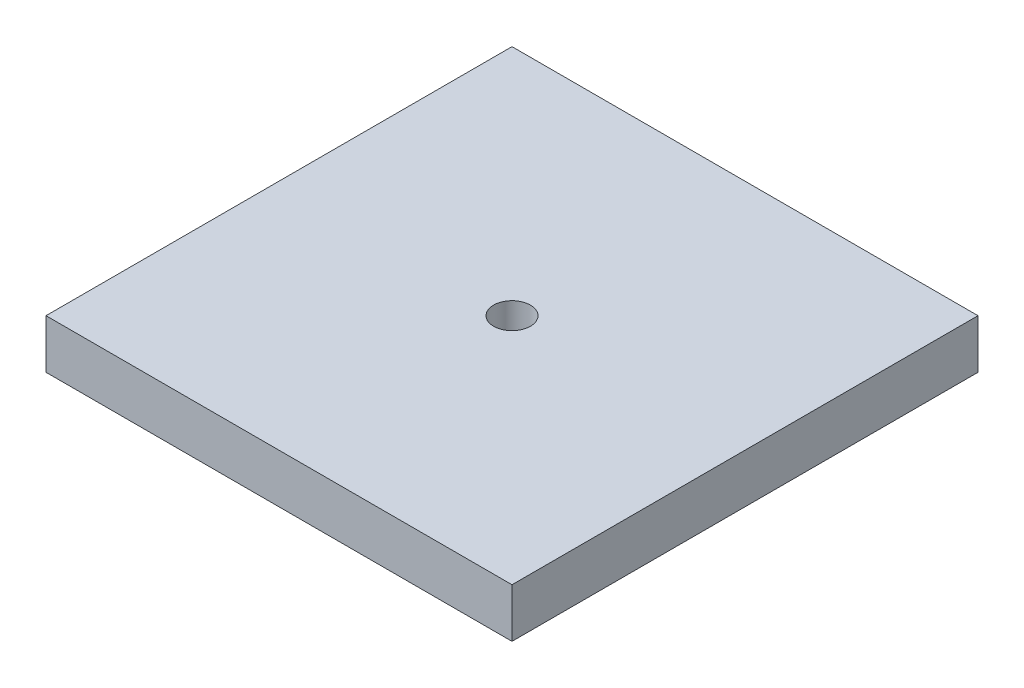
SolidWorks part; units mm, degrees
ref_plane "Front Plane" through (0, 0, 0) normal (0, 0, 1) x (1, 0, 0)
ref_plane "Top Plane" through (0, 0, 0) normal (0, 1, 0) x (1, 0, 0)
ref_plane "Right Plane" through (0, 0, 0) normal (1, 0, 0) x (0, 0, -1)
sketch "Sketch1" plane through (0, 0, 0) normal (0, 1, 0) x (1, 0, 0)
  line L1 (0, 0) -> (15.2, 0)
  line L2 (0, 0) -> (0, 15.2)
  line L3 (0, 15.2) -> (15.2, 15.2)
  line L4 (15.2, 0) -> (15.2, 15.2)
  dimension "D1" = 15.2
  dimension "D2" = 15.2
extrude "Boss-Extrude1" add sketch "Sketch1" along normal blind 1.6 contours L2 L1 L4 L3
sketch "Sketch2" plane through (0, 1.6, 0) normal (0, 1, 0) x (1, 0, 0)
  line L0 (0, 7.6) -> (15.2, 7.6) construction
  line L1 (0, 0) -> (0, 15.2) construction
  line L2 (15.2, 0) -> (15.2, 15.2) construction
  line L3 (7.6, 7.6) -> (7.6, 15.2) construction
  line L4 (0, 15.2) -> (15.2, 15.2) construction
  circle A0 centre (7.6, 7.6) radius 0.6
  dimension "D1" = 1.2
extrude "Cut-Extrude1" cut sketch "Sketch2" against normal blind 5
